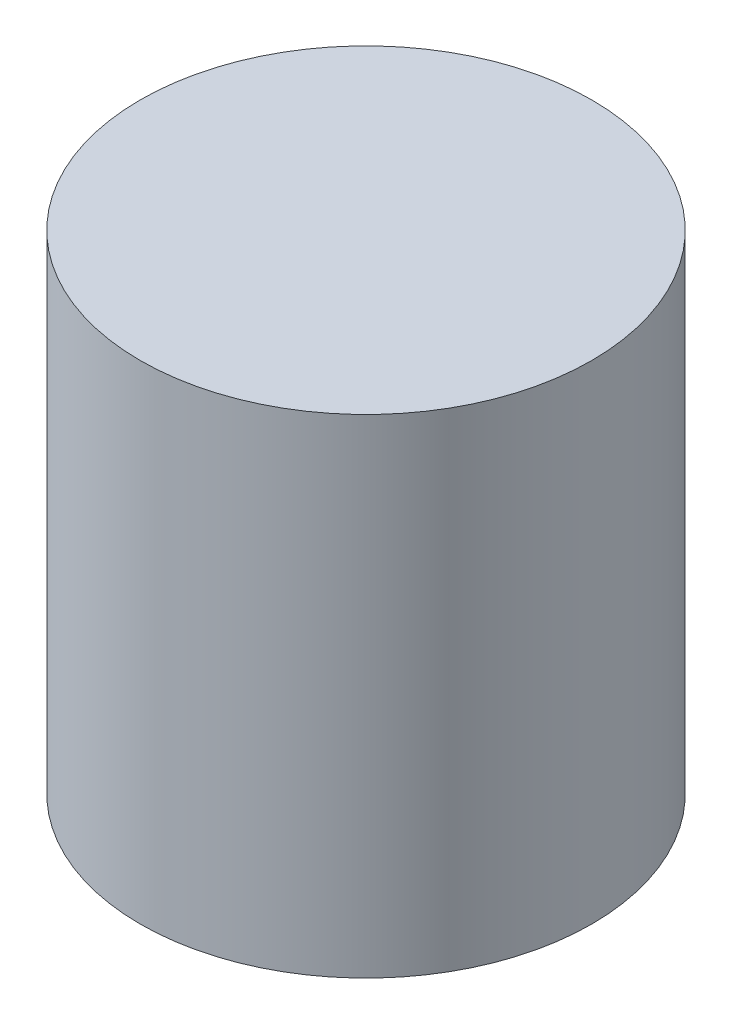
SolidWorks part; units mm, degrees
ref_plane "Front Plane" through (0, 0, 0) normal (0, 0, 1) x (1, 0, 0)
ref_plane "Top Plane" through (0, 0, 0) normal (0, 1, 0) x (1, 0, 0)
ref_plane "Right Plane" through (0, 0, 0) normal (1, 0, 0) x (0, 0, -1)
sketch "Sketch1" plane through (0, 0, 0) normal (0, 1, 0) x (1, 0, 0)
  circle A0 centre (0, 0) radius 18.5
  dimension "D1" = 37
extrude "Boss-Extrude1" add sketch "Sketch1" along normal blind 40
